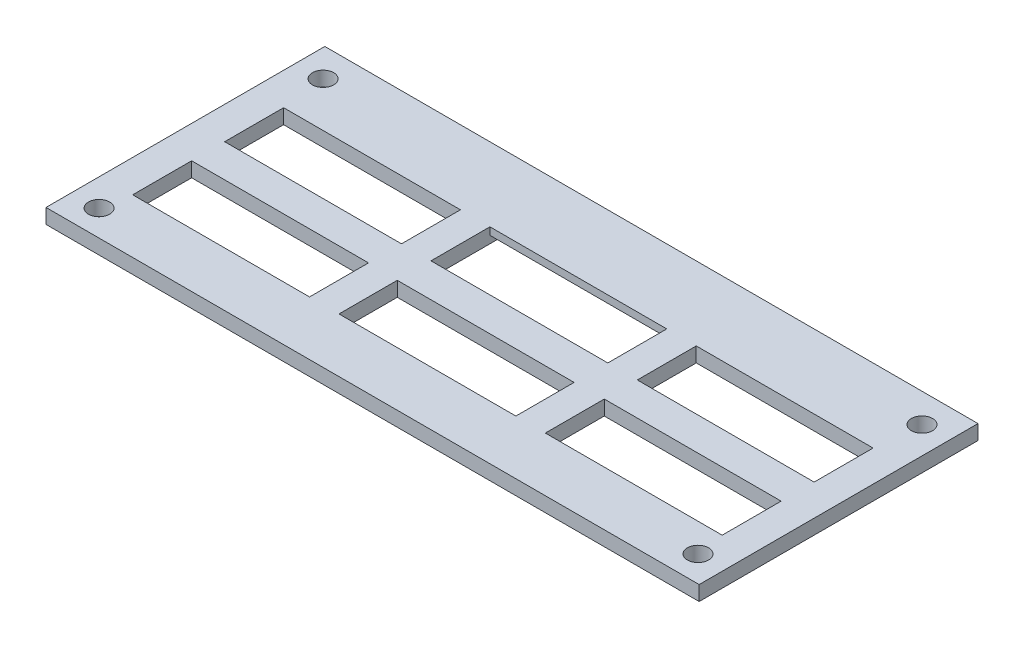
SolidWorks part; units mm, degrees
material "ABS"
ref_plane "Front Plane" through (0, 0, 0) normal (0, 0, 1) x (1, 0, 0)
ref_plane "Top Plane" through (0, 0, 0) normal (0, 1, 0) x (1, 0, 0)
ref_plane "Right Plane" through (0, 0, 0) normal (1, 0, 0) x (0, 0, -1)
sketch "Sketch3" plane through (0, 0, 0) normal (0, 1, 0) x (1, 0, 0)
  line L0 (-69.6627, 37.9615) -> (-18.2292, 37.9615)
  line L1 (-69.6627, 37.9615) -> (-69.6627, 22.0934)
  line L2 (-69.6627, 22.0934) -> (-18.2292, 22.0934)
  line L3 (-18.2292, 37.9615) -> (-18.2292, 22.0934)
  line L4 (-18.2292, 22.0934) -> (-24.5792, 22.0934)
  line L5 (-18.2292, 22.0934) -> (-18.2292, -10.4186)
  line L6 (-18.2292, -10.4186) -> (-24.5792, -10.4186)
  line L7 (-24.5792, 22.0934) -> (-24.5792, -10.4186)
  line L8 (19.8708, 22.0934) -> (26.2208, 22.0934)
  line L9 (19.8708, 22.0934) -> (19.8708, -10.4186)
  line L10 (19.8708, -10.4186) -> (26.2208, -10.4186)
  line L11 (26.2208, 22.0934) -> (26.2208, -10.4186)
  line L12 (64.3208, 9.3934) -> (26.2208, 9.3934)
  line L13 (64.3208, 9.3934) -> (64.3208, 2.2814)
  line L14 (64.3208, 2.2814) -> (26.2208, 2.2814)
  line L15 (26.2208, 9.3934) -> (26.2208, 2.2814)
  line L16 (-18.2292, 9.3934) -> (19.8708, 9.3934)
  line L17 (-18.2292, 9.3934) -> (-18.2292, 2.1301)
  line L18 (-18.2292, 2.1301) -> (19.8708, 2.1301)
  line L19 (19.8708, 9.3934) -> (19.8708, 2.1301)
  line L20 (19.8708, 37.9615) -> (-18.2292, 37.9615)
  line L21 (19.8708, 37.9615) -> (19.8708, 31.6917)
  line L22 (19.8708, 31.6917) -> (-18.2292, 31.6917)
  line L23 (-18.2292, 37.9615) -> (-18.2292, 31.6917)
  line L24 (-69.6627, -22.1095) -> (-62.6792, -22.1095)
  line L25 (-69.6627, -22.1095) -> (-69.6627, 22.0934)
  line L26 (-69.6627, 22.0934) -> (-62.6792, 22.0934)
  line L27 (-62.6792, -22.1095) -> (-62.6792, 22.0934)
  line L28 (71.0533, -22.1095) -> (64.3208, -22.1095)
  line L29 (71.0533, -22.1095) -> (71.0533, 22.0934)
  line L30 (71.0533, 22.0934) -> (64.3208, 22.0934)
  line L31 (64.3208, -22.1095) -> (64.3208, 22.0934)
  line L32 (64.3208, -10.4186) -> (-62.6792, -10.4186)
  line L33 (64.3208, -10.4186) -> (64.3208, -22.1095)
  line L34 (64.3208, -22.1095) -> (-62.6792, -22.1095)
  line L35 (-62.6792, -10.4186) -> (-62.6792, -22.1095)
  line L36 (-24.5792, 9.3934) -> (-62.6792, 9.3934)
  line L37 (-24.5792, 9.3934) -> (-24.5792, 2.2814)
  line L38 (-24.5792, 2.2814) -> (-62.6792, 2.2814)
  line L39 (-62.6792, 9.3934) -> (-62.6792, 2.2814)
  line L40 (19.8708, 22.0934) -> (71.0533, 22.0934)
  line L41 (19.8708, 22.0934) -> (19.8708, 37.9615)
  line L42 (19.8708, 37.9615) -> (71.0533, 37.9615)
  line L43 (71.0533, 22.0934) -> (71.0533, 37.9615)
  line L45 (-18.2292, 22.0934) -> (19.8708, 22.0934)
  line L46 (-18.2292, 22.0934) -> (-18.2292, 31.6917)
  line L47 (-18.2292, 31.6917) -> (19.8708, 31.6917)
  line L48 (19.8708, 22.0934) -> (19.8708, 31.6917)
  circle A0 centre (-63.8207, 31.7385) radius 2.286
  circle A1 centre (-63.8207, -16.5215) radius 2.286
  circle A2 centre (65.2113, 31.7385) radius 2.286
  circle A3 centre (65.2113, -16.5215) radius 2.286
extrude "Boss-Extrude1" add sketch "Sketch3" along normal blind 3.175
sketch "Sketch4" plane through (0, 3.175, 0) normal (0, 1, 0) x (1, 0, 0)
  line L0 (19.8708, 31.6917) -> (19.8708, 9.3934) construction
  line L1 (-18.2292, 31.6917) -> (19.8708, 31.6917)
  line L2 (-18.2292, 31.6917) -> (-18.2292, 22.0934)
  line L3 (-18.2292, 22.0934) -> (19.8708, 22.0934)
  line L4 (19.8708, 31.6917) -> (19.8708, 22.0934)
extrude "Boss-Extrude2" add sketch "Sketch4" against normal blind 1.5875
